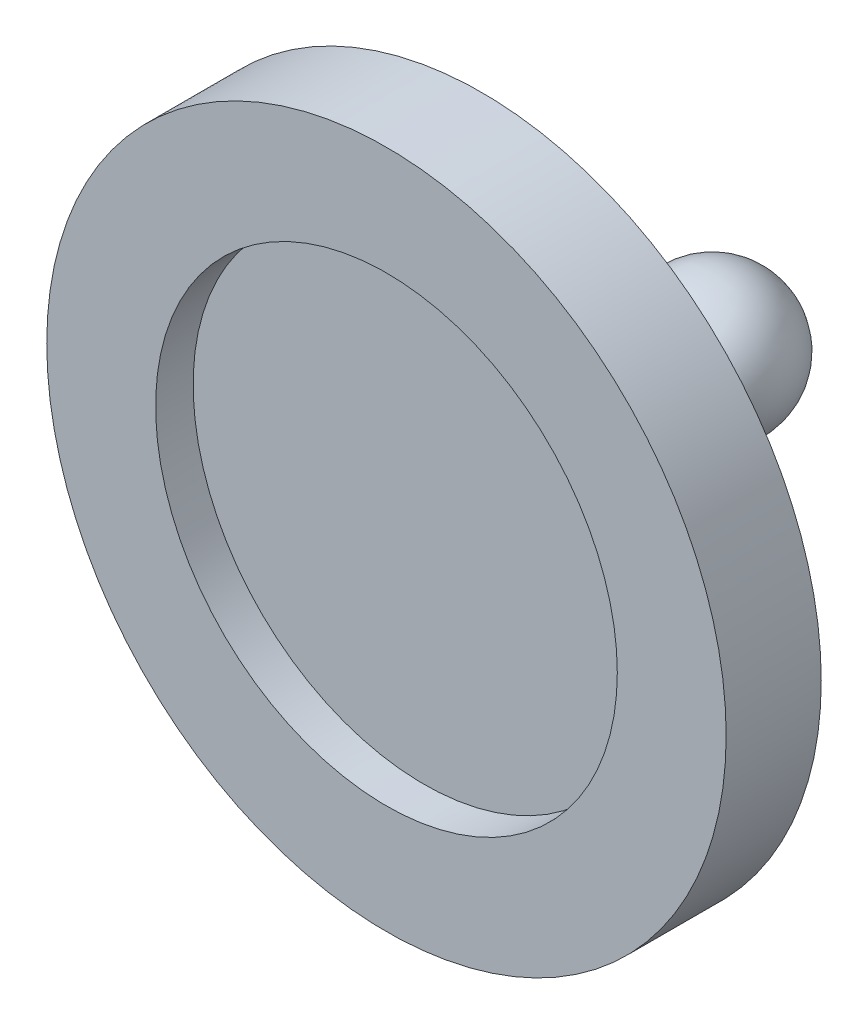
SolidWorks part; units mm, degrees
ref_plane "Front Plane" through (0, 0, 0) normal (0, 0, 1) x (1, 0, 0)
ref_plane "Top Plane" through (0, 0, 0) normal (0, 1, 0) x (1, 0, 0)
ref_plane "Right Plane" through (0, 0, 0) normal (1, 0, 0) x (0, 0, -1)
sketch "Sketch2" plane through (0, 0, 0) normal (0, 1, 0) x (1, 0, 0)
  line L0 (0, 0) -> (0, 23.3202) construction
  line L1 (2.2869, 17.8832) -> (10.6021, 9.568)
  line L2 (10.6021, 9.568) -> (15.6021, 9.568)
  line L4 (15.6021, 5.2012) -> (10.6021, 5.2012)
  line L5 (0, 6.9241) -> (0, 23.4043)
  line L6 (10.6021, 5.2012) -> (10.6021, 6.9241)
  line L7 (10.6021, 6.9241) -> (0, 6.9241)
  line L8 (15.6021, 9.568) -> (15.6021, 5.2012)
  arc A0 (2.2869, 17.8832) -> (0, 23.4043) centre (0, 20.1701) ccw
revolve "Revolve1" add sketch "Sketch2" angle 360 about L0
